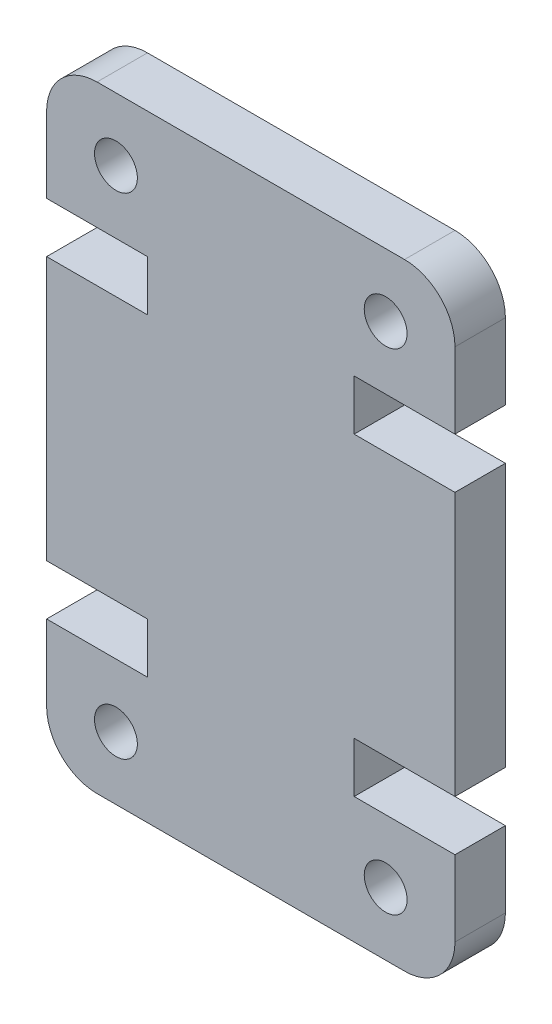
SolidWorks part; units mm, degrees
ref_plane "Front Plane" through (0, 0, 0) normal (0, 0, 1) x (1, 0, 0)
ref_plane "Top Plane" through (0, 0, 0) normal (0, 1, 0) x (1, 0, 0)
ref_plane "Right Plane" through (0, 0, 0) normal (1, 0, 0) x (0, 0, -1)
sketch "Sketch1" plane through (0, 0, 0) normal (0, 0, 1) x (1, 0, 0)
  line L0 (0, 17.45) -> (0, 7)
  line L1 (16.2, 5) -> (16.2, 2)
  line L2 (12.2, 5) -> (16.2, 5)
  line L3 (2, 0) -> (14.2, 0)
  line L4 (16.2, 7) -> (12.2, 7)
  line L5 (12.2, 7) -> (12.2, 5)
  line L6 (16.2, 17.45) -> (16.2, 7)
  line L7 (0, 19.45) -> (0, 22.45)
  line L8 (4, 19.45) -> (0, 19.45)
  line L9 (0, 17.45) -> (4, 17.45)
  line L10 (4, 7) -> (4, 5)
  line L11 (4, 17.45) -> (4, 19.45)
  line L12 (0, 7) -> (4, 7)
  line L13 (4, 5) -> (0, 5)
  line L14 (12.2, 17.45) -> (12.2, 19.45)
  line L15 (16.2, 17.45) -> (12.2, 17.45)
  line L16 (2, 24.45) -> (14.2, 24.45)
  line L17 (12.2, 19.45) -> (16.2, 19.45)
  line L18 (16.2, 19.45) -> (16.2, 22.45)
  line L19 (0, 5) -> (0, 2)
  line L20 (0, 12.225) -> (16.2, 12.225) construction
  line L21 (8.1, 24.45) -> (8.1, 0) construction
  circle A0 centre (13.45, 2.5) radius 0.85
  arc A1 (16.2, 2) -> (14.2, 0) centre (14.2, 2) cw
  circle A2 centre (2.75, 21.95) radius 0.85
  arc A3 (0, 2) -> (2, 0) centre (2, 2) ccw
  arc A4 (0, 22.45) -> (2, 24.45) centre (2, 22.45) cw
  circle A5 centre (2.75, 2.5) radius 0.85
  arc A6 (16.2, 22.45) -> (14.2, 24.45) centre (14.2, 22.45) ccw
  circle A7 centre (13.45, 21.95) radius 0.85
  point P17 (8.1, 12.225)
  dimension "D1" = 1.7
  dimension "D2" = 2
  dimension "D3" = 2.75
  dimension "D4" = 8.1
  dimension "D5" = 2.5
  dimension "D6" = 5
  dimension "D8" = 12.225
extrude "Boss-Extrude1" add sketch "Sketch1" along normal blind 4
sketch "Sketch2" plane through (0, 0, 0) normal (0, 0, -1) x (-1, 0, 0)
  line L0 (0, 0) -> (0, 24.45)
  line L1 (0, 24.45) -> (-16.2, 24.45)
  line L2 (-16.2, 24.45) -> (-16.2, 0)
  line L3 (-16.2, 0) -> (0, 0)
extrude "Cut-Extrude1" cut sketch "Sketch2" against normal blind 2
equation "\"D4@Sketch1\"= \"fingerWidth@parametersSketch@prostheticParameters.SLDPRT\" / 2 'MIP Width"
equation "\"D8@Sketch1\"= ( ( \"HL@parametersSketch@prostheticParameters.SLDPRT\" * 0.17 ) - 4 - 3 ) / 2 'MIP Length - Sil. Sht MIP - Sil. Sht DIP"
equation "\"D1@Sketch1\"= 1.5 + \"tol1@parametersSketch@prostheticParameters.SLDPRT\""
